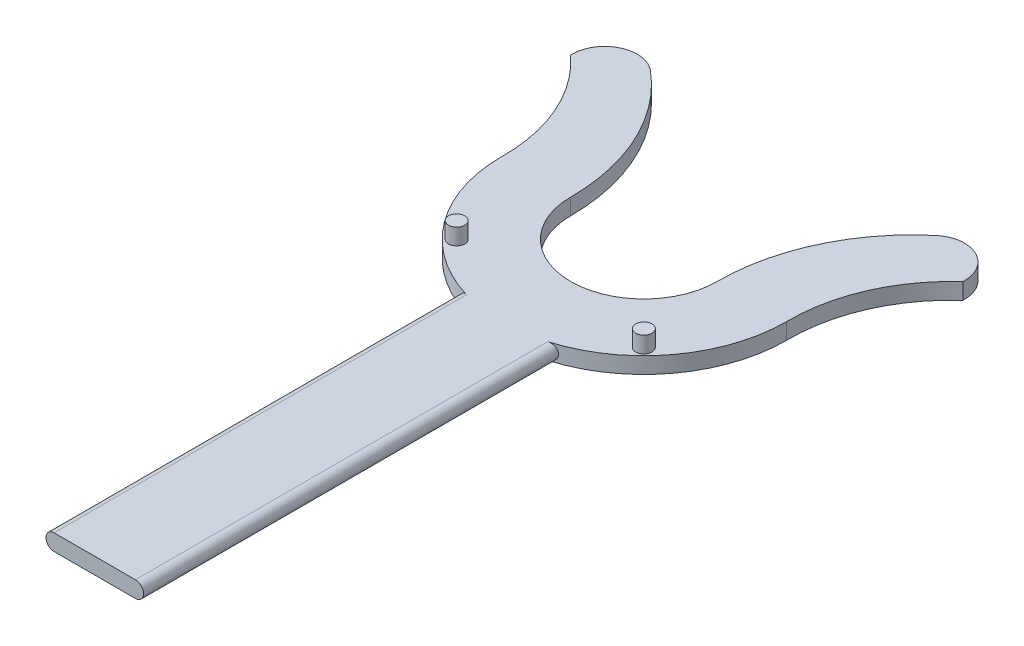
SolidWorks part; units mm, degrees
ref_plane "Front Plane" through (0, 0, 0) normal (0, 0, 1) x (1, 0, 0)
ref_plane "Top Plane" through (0, 0, 0) normal (0, 1, 0) x (1, 0, 0)
ref_plane "Right Plane" through (0, 0, 0) normal (1, 0, 0) x (0, 0, -1)
sketch "Sketch1" plane through (0, 0, 0) normal (0, 1, 0) x (1, 0, 0)
  line L0 (-22.5, 0) -> (0, 0) construction
  line L1 (-43.8683, 0) -> (-22.5, 0) construction
  line L3 (0, 0) -> (0, -43.8683) construction
  arc A0 (-22.5, 0) -> (22.5, 0) centre (0, 0) ccw
  arc A1 (-22.5, 0) -> (-43.9055, 45.9398) centre (-82.5, 0) ccw
  arc A2 (-43.9055, 45.9398) -> (-60.3252, 37.779) centre (-50.3379, 38.2832) ccw
  arc A3 (-60.3252, 37.779) -> (-43.8683, 0) centre (-93.8635, 0.6956) cw
  arc A4 (-43.8683, 0) -> (43.8683, 0) centre (0, 0) ccw
  arc A5 (60.3252, 37.779) -> (43.8683, 0) centre (93.8635, 0.6956) ccw
  arc A6 (43.9055, 45.9398) -> (60.3252, 37.779) centre (50.3379, 38.2832) cw
  arc A7 (22.5, 0) -> (43.9055, 45.9398) centre (82.5, 0) cw
  circle A8 centre (0, 0) radius 38.1 construction
  dimension "D1" = 45
  dimension "D2" = 60
  dimension "D3" = 10
  dimension "D5" = 16.4197
  dimension "D6" = 50
  dimension "D8" = 43.8683
  dimension "D9" = 76.2
  dimension "D4" = 8.1608
  dimension "D7" = 16.4569
extrude "Boss-Extrude1" add sketch "Sketch1" along normal blind 5
sketch "Sketch2" plane through (0, 5, 0) normal (0, 1, 0) x (1, 0, 0)
  line L0 (0, 0) -> (0, -43.8683) construction
  line L1 (-43.8683, -43.8683) -> (43.8683, -43.8683) construction
  line L2 (-43.8683, -43.8683) -> (0, 0) construction
  line L3 (0, 0) -> (43.8683, -43.8683) construction
  arc A0 (-43.8683, 0) -> (43.8683, 0) centre (0, 0) ccw construction
  circle A2 centre (0, 0) radius 38.2 construction
  circle A3 centre (28.7792, -28.7792) radius 2.5
  circle A4 centre (-28.7792, -28.7792) radius 2.5
  dimension "D1" = 45
  dimension "D2" = 76.4
  dimension "D3" = 5
  dimension "D4" = 5
extrude "Boss-Extrude2" add sketch "Sketch2" along normal blind 5
ref_plane "Plane1" through (0, 5, 43.8683) normal (0, 0, 1) x (1, 0, 0)
sketch "Sketch4" plane through (0, 5, 43.8683) normal (0, 0, 1) x (1, 0, 0)
  line L0 (0, -5) -> (0, 0) construction
  line L5 (12.5, -2.5) -> (-12.5, -2.5) construction
  line L6 (12.5, -5) -> (-12.5, -5)
  line L7 (12.5, 0) -> (-12.5, 0)
  arc A0 (12.5, -5) -> (12.5, 0) centre (12.5, -2.5) ccw
  arc A1 (-12.5, 0) -> (-12.5, -5) centre (-12.5, -2.5) ccw
  point P4 (0, -2.5)
  dimension "D1" = 25
extrude "Boss-Extrude3" add sketch "Sketch4" along normal blind 125 and the other way up to surface
